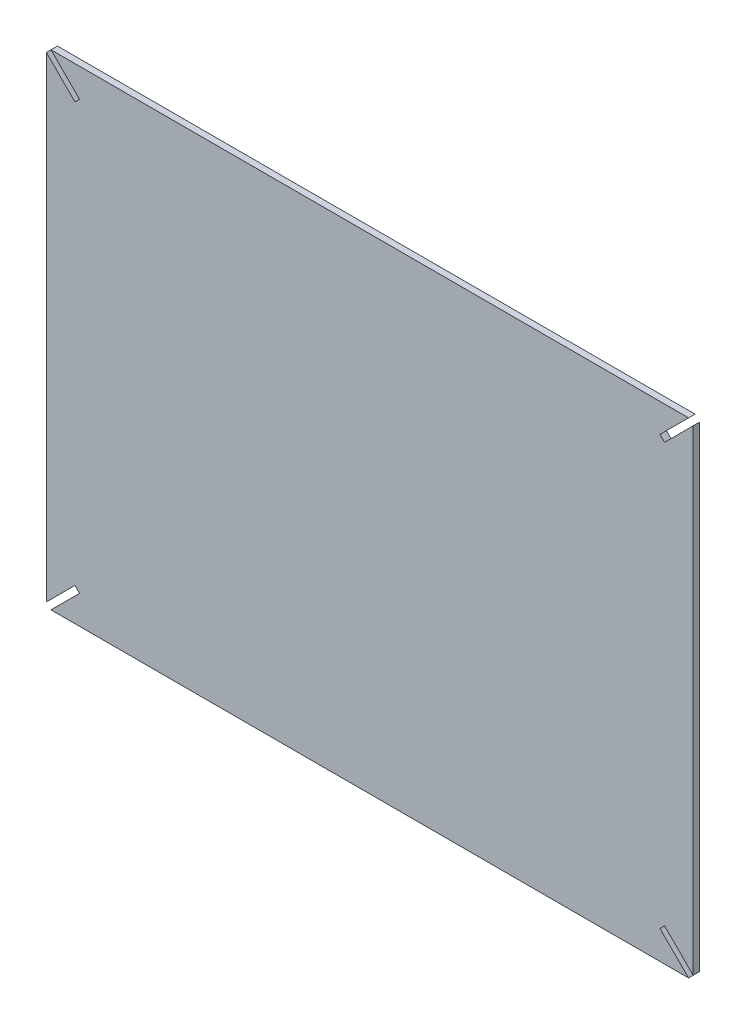
SolidWorks part; units mm, degrees
ref_plane "Plan de face" through (0, 0, 0) normal (0, 0, 1) x (1, 0, 0)
ref_plane "Plan de dessus" through (0, 0, 0) normal (0, 1, 0) x (1, 0, 0)
ref_plane "Plan de droite" through (0, 0, 0) normal (1, 0, 0) x (0, 0, -1)
sketch "Esquisse1" plane through (0, 0, 0) normal (0, 0, 1) x (1, 0, 0)
  line L0 (-435.113, 131.2491) -> (-40.7699, 131.2491)
  line L1 (-437.9415, 131.2491) -> (-37.9415, 131.2491) construction
  line L2 (-437.9415, 131.2491) -> (-437.9415, -168.7509) construction
  line L3 (-437.9415, -168.7509) -> (-37.9415, -168.7509) construction
  line L4 (-37.9415, 131.2491) -> (-37.9415, -168.7509) construction
  line L5 (-437.9415, 128.4207) -> (-437.9415, -165.9225)
  line L6 (-435.113, -168.7509) -> (-40.7699, -168.7509)
  line L7 (-37.9415, -165.9225) -> (-37.9415, 128.4207)
  line L8 (-37.9415, 128.4207) -> (-55.6191, 110.743)
  line L9 (-55.6191, 110.743) -> (-58.4476, 113.5714)
  line L10 (-58.4476, 113.5714) -> (-40.7699, 131.2491)
  line L11 (-37.9415, -165.9225) -> (-55.6191, -148.2448)
  line L12 (-55.6191, -148.2448) -> (-58.4476, -151.0732)
  line L13 (-58.4476, -151.0732) -> (-40.7699, -168.7509)
  line L14 (-435.113, -168.7509) -> (-417.4354, -151.0732)
  line L15 (-417.4354, -151.0732) -> (-420.2638, -148.2448)
  line L16 (-420.2638, -148.2448) -> (-437.9415, -165.9225)
  line L17 (-435.113, 131.2491) -> (-417.4354, 113.5714)
  line L18 (-417.4354, 113.5714) -> (-420.2638, 110.743)
  line L19 (-420.2638, 110.743) -> (-437.9415, 128.4207)
  dimension "D1" = 300
  dimension "D2" = 400
  dimension "D3" = 4
  dimension "D4" = 25
  dimension "D5" = 45
  dimension "D6" = 45
  dimension "D7" = 45
  dimension "D8" = 45
extrude "Boss.-Extru.1" add sketch "Esquisse1" along normal blind 4
